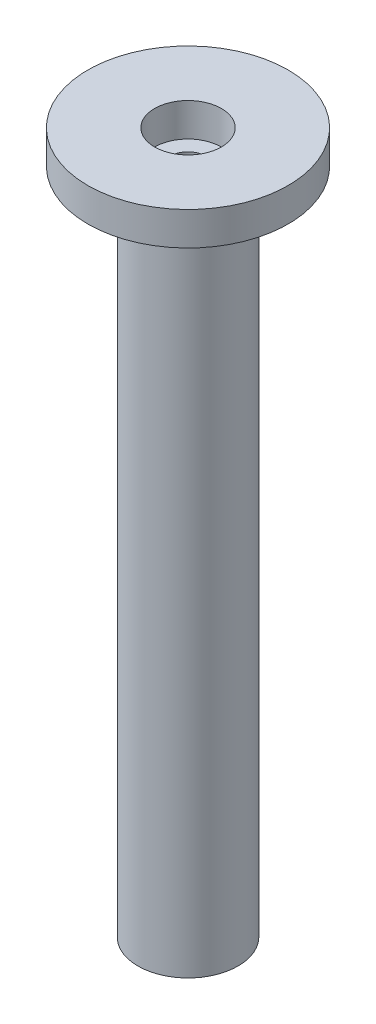
SolidWorks part; units mm, degrees
ref_plane "Front Plane" through (0, 0, 0) normal (0, 0, 1) x (1, 0, 0)
ref_plane "Top Plane" through (0, 0, 0) normal (0, 1, 0) x (1, 0, 0)
ref_plane "Right Plane" through (0, 0, 0) normal (1, 0, 0) x (0, 0, -1)
sketch "Sketch1" plane through (0, 0, 0) normal (0, 1, 0) x (1, 0, 0)
  circle A0 centre (0, 0) radius 9.525
  dimension "D1" = 19.05
extrude "Boss-Extrude1" add sketch "Sketch1" along normal blind 127
sketch "Sketch2" plane through (0, 127, 0) normal (0, 1, 0) x (1, 0, 0)
  circle A0 centre (0, 0) radius 19.05
  dimension "D1" = 38.1
extrude "Boss-Extrude2" add sketch "Sketch2" along normal blind 6.35
sketch "Sketch3" plane through (0, 133.35, 0) normal (0, 1, 0) x (1, 0, 0)
  circle A1 centre (0, 0) radius 6.35
  dimension "D2" = 12.7
extrude "Cut-Extrude1" cut sketch "Sketch3" against normal blind 6.35
sketch "Sketch4" plane through (0, 0, 0) normal (0, -1, 0) x (1, 0, 0)
  circle A0 centre (0, 0) radius 6.35
  dimension "D1" = 12.7
extrude "Cut-Extrude2" cut sketch "Sketch4" against normal blind 6.35
sketch "Sketch5" plane through (0, 6.35, 0) normal (0, -1, 0) x (1, 0, 0)
  circle A0 centre (0, 0) radius 3.3734
  dimension "D1" = 6.7469
extrude "Cut-Extrude3" cut sketch "Sketch5" against normal through all
